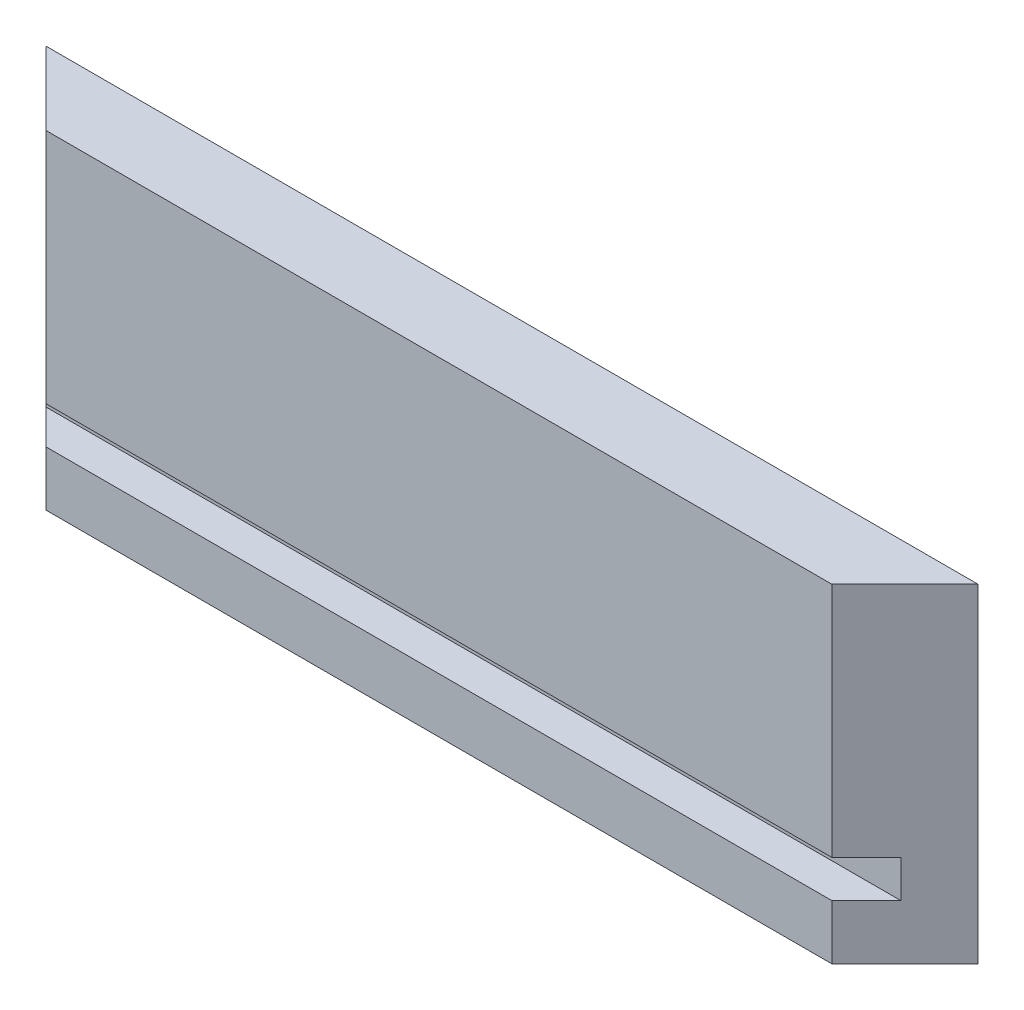
SolidWorks part; units mm, degrees
material "Beech"
ref_plane "Front Plane" through (0, 0, 0) normal (0, 0, 1) x (1, 0, 0)
ref_plane "Top Plane" through (0, 0, 0) normal (0, 1, 0) x (1, 0, 0)
ref_plane "Right Plane" through (0, 0, 0) normal (1, 0, 0) x (0, 0, -1)
other "Configuration Table"
sketch "Sketch1" plane through (0, 0, 0) normal (0, 1, 0) x (1, 0, 0)
  line L0 (0, 0) -> (81.0006, 0)
  line L1 (81.0006, 0) -> (74.6506, -6.35)
  line L2 (74.6506, -6.35) -> (6.35, -6.35)
  line L3 (6.35, -6.35) -> (0, 0)
  dimension "D1" = 45
  dimension "D2" = 45
  dimension "D3" = 81.0006
  dimension "D4" = 6.35
extrude "Boss-Extrude1" add sketch "Sketch1" along normal blind 28.575
sketch "Sketch2" plane through (0, 0, 0) normal (1, 0, 0) x (0, 0, -1)
  line L0 (-6.35, 4.7625) -> (-3.3528, 4.7625)
  line L1 (-6.35, 28.575) -> (-6.35, 0) construction
  line L2 (-3.3528, 4.7625) -> (-3.3528, 8.0137)
  line L3 (-3.3528, 8.0137) -> (-6.35, 8.0137)
  line L4 (-6.35, 8.0137) -> (-6.35, 4.7625)
  line L5 (-6.35, 0) -> (0, 0) construction
  dimension "D1" = 4.7625
  dimension "D2" = 3.2512
  dimension "D3" = 2.9972
extrude "Cut-Extrude1" cut sketch "Sketch2" along normal through all both and the other way through all
